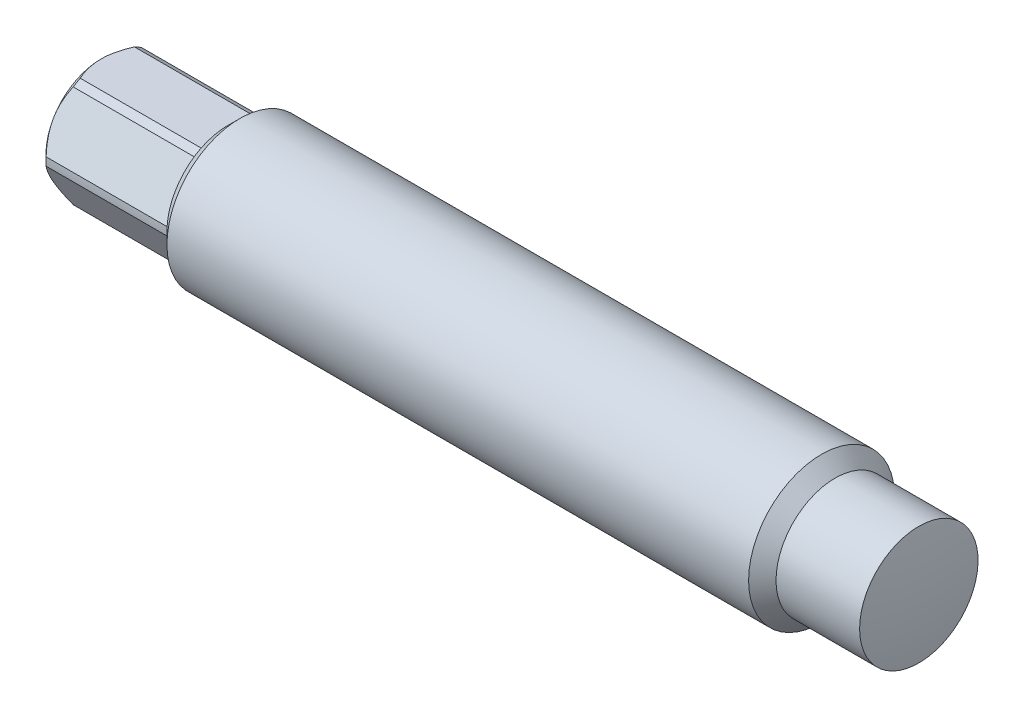
SolidWorks part; units mm, degrees
material "NITRONIC 60"
ref_plane "Front" through (0, 0, 0) normal (0, 0, 1) x (1, 0, 0)
ref_plane "Top" through (0, 0, 0) normal (0, 1, 0) x (1, 0, 0)
ref_plane "Right" through (0, 0, 0) normal (1, 0, 0) x (0, 0, -1)
sketch "Sketch1 w/mock PCB" plane through (0, 0, 0) normal (0, 0, 1) x (1, 0, 0)
  line L0 (0, 0) -> (-106.68, 0)
  line L1 (-0.5844, 7.6835) -> (-11.43, 7.6835)
  line L2 (-11.43, 7.6835) -> (-13.208, 9.4615)
  line L3 (0, 0) -> (10.8456, 0) construction
  line L4 (-13.208, 9.4615) -> (-88.6714, 9.4615)
  line L6 (-88.6714, 9.4615) -> (-90.17, 7.9629)
  line L7 (-90.17, 7.9629) -> (-105.8609, 7.9629)
  line L8 (-106.68, 7.1437) -> (-106.68, 0)
  line L9 (-105.8609, 7.9629) -> (-106.68, 7.1437)
  arc A0 (0, 0) -> (-0.5844, 7.6835) centre (-50.8, 0) ccw
  point P5 (-25.908, 20.828)
  point P6 (25.908, 20.828)
  point P7 (25.908, -20.828)
  point P8 (-25.908, -20.828)
  point P63 (-25.781, -19.05)
  point P64 (25.781, -19.05)
  dimension "D5" = 18.923
  dimension "D6" = 15.9258
  dimension "D7" = 16.51
  dimension "D8" = 106.68
  dimension "D9" = 14.2875
  dimension "D3" = 50.8
  dimension "D1" = 45
  dimension "D2" = 15.367
  dimension "D4" = 11.43
revolve "Revolve1" add sketch "Sketch1 w/mock PCB" angle 360 about L3
ref_plane "Hex Plane" through (-90.17, 0, 0) normal (1, 0, 0) x (0, 0, -1)
sketch "Sketch1" plane through (-90.17, 0, 0) normal (1, 0, 0) x (0, 0, -1)
  line L1 (4.1244, 7.1438) -> (-4.1244, 7.1437)
  line L2 (-4.1244, 7.1437) -> (-8.2489, 0)
  line L3 (-8.2489, 0) -> (-4.1244, -7.1438)
  line L4 (-4.1244, -7.1438) -> (4.1244, -7.1438)
  line L5 (4.1244, -7.1438) -> (8.2489, 0)
  line L6 (8.2489, 0) -> (4.1244, 7.1438)
  circle A0 centre (0, 0) radius 7.1438 construction
  dimension "D1" = 14.2875
extrude "Cut-Extrude1" cut sketch "Sketch1" against normal through all flip side to cut
sketch "Sketch2" plane through (0, 0, 0) normal (0, 0, 1) x (1, 0, 0)
  line L0 (-98.464, 0) -> (-99.3806, 1.5875)
  line L1 (-99.3806, 1.5875) -> (-102.5556, 1.5875)
  line L2 (-102.5556, 1.5875) -> (-106.68, 3.9688)
  line L3 (-98.464, 0) -> (-106.68, 0)
  line L4 (-106.68, 0) -> (-106.68, 3.9688)
  line L5 (-106.68, 0) -> (-114.896, 0) construction
  line L6 (-98.464, 0) -> (-99.3806, -1.5875) construction
  line L7 (-102.5556, -1.5875) -> (-106.68, -3.9687) construction
  line L8 (-106.68, 7.1437) -> (-106.68, 0) construction
  dimension "D1" = 120
  dimension "D2" = 3.175
  dimension "D3" = 3.175
  dimension "D4" = 60
  dimension "D5" = 7.9375
revolve "Cut-Revolve1" cut sketch "Sketch2" angle 360 about L5
